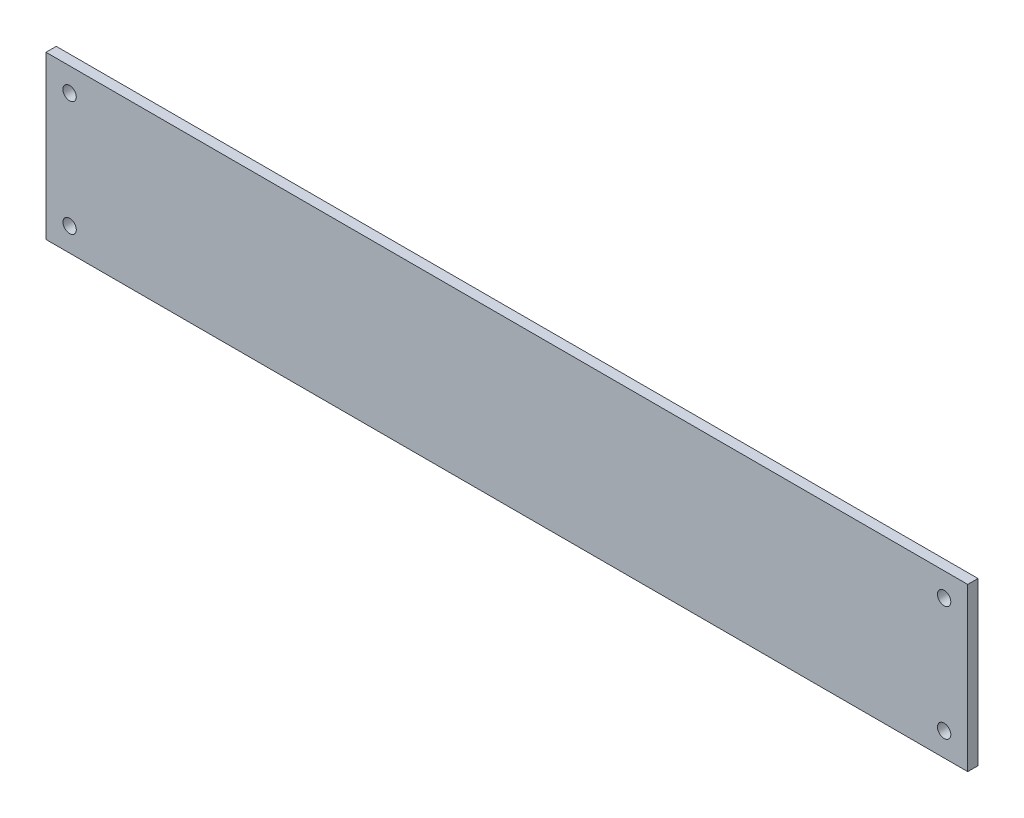
SolidWorks part; units mm, degrees
ref_plane "Piano frontale" through (0, 0, 0) normal (0, 0, 1) x (1, 0, 0)
ref_plane "Piano superiore" through (0, 0, 0) normal (0, 1, 0) x (1, 0, 0)
ref_plane "Piano destro" through (0, 0, 0) normal (1, 0, 0) x (0, 0, -1)
sketch "f" plane through (0, 0, 0) normal (0, 0, 1) x (1, 0, 0)
  line L0 (0, 0) -> (0, 79)
  line L1 (0, 79) -> (449, 79)
  line L2 (449, 79) -> (449, 0)
  line L3 (449, 0) -> (0, 0)
  line L4 (0, 39.5) -> (449, 39.5) construction
  line L5 (224.5, 42) -> (224.5, 123.488) construction
  line L10 (449, 79) -> (224.5, 0) construction
  line L11 (334, 39.5) -> (334, 81.5) construction
  line L12 (224.5, 0) -> (0, 79) construction
  line L13 (112.25, 42) -> (112.25, 84) construction
  circle A0 centre (11.5, 67.5) radius 3.25
  circle A1 centre (437.5, 67.5) radius 3.25
  circle A2 centre (11.5, 11.5) radius 3.25
  circle A3 centre (437.5, 11.5) radius 3.25
  dimension "D3" = 11.5
  dimension "D4" = 11.5
  dimension "D5" = 6.5
  dimension "D1" = 79
  dimension "D2" = 449
extrude "Estrusione-Estrusione1" add sketch "f" along normal blind 5
